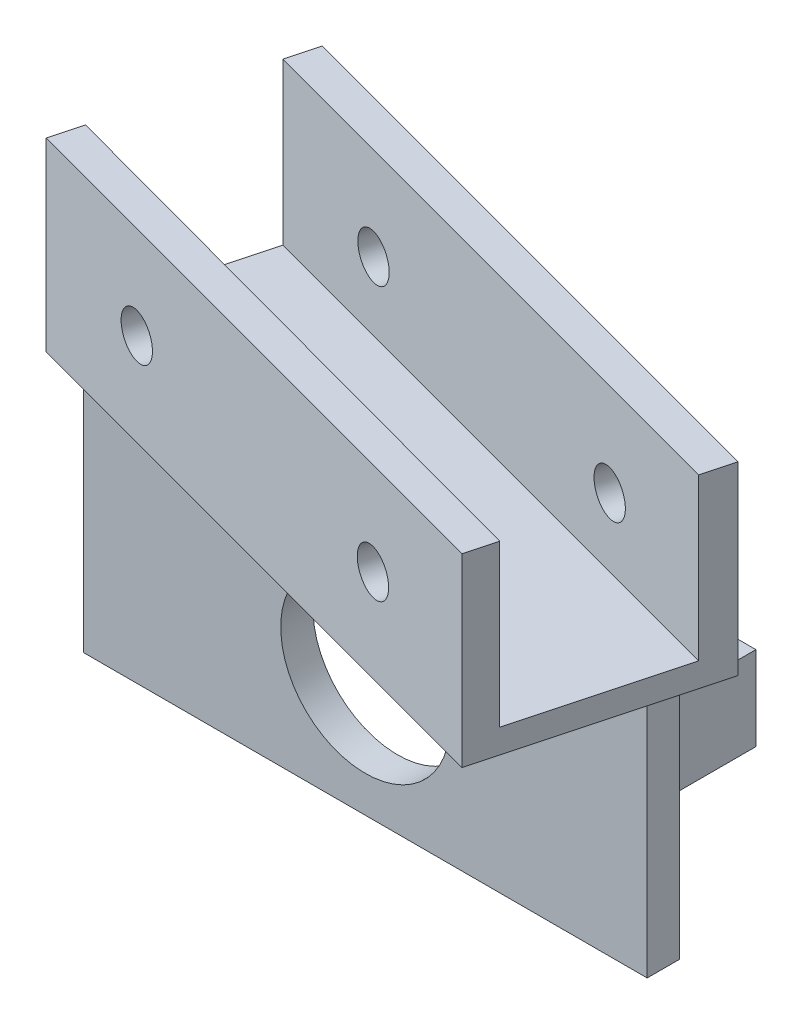
SolidWorks part; units mm, degrees
ref_plane "Front Plane" through (0, 0, 0) normal (0, 0, 1) x (1, 0, 0)
ref_plane "Top Plane" through (0, 0, 0) normal (0, 1, 0) x (1, 0, 0)
ref_plane "Right Plane" through (0, 0, 0) normal (1, 0, 0) x (0, 0, -1)
sketch "Sketch1" plane through (0, 0, 0) normal (0, 0, 1) x (1, 0, 0)
  line L1 (0, 0) -> (70, 0)
  line L2 (0, 0) -> (0, -30)
  line L3 (0, -30) -> (70, -30)
  line L4 (70, 0) -> (70, -30)
  circle A0 centre (35, -15) radius 10.5
  point P7 (70, -15)
  point P8 (35, -30)
  dimension "D1" = 21
  dimension "D2" = 30
  dimension "D3" = 70
extrude "Boss-Extrude1" add sketch "Sketch1" along normal blind 4
sketch "Sketch3" plane through (0, 0, 0) normal (0, 0, -1) x (-1, 0, 0)
  line L0 (-62.5, -8.9384) -> (-54.349, -8.9384)
  line L1 (-54.349, -8.9384) -> (-54.349, -19.3738)
  line L2 (-54.349, -19.3738) -> (-62.5, -19.3738)
  line L3 (-7.5, -5) -> (-14.3209, -5)
  line L4 (-7.5, -25) -> (-7.5, -5)
  line L5 (-62.5, -25) -> (-7.5, -25)
  line L6 (-62.5, -5) -> (-62.5, -25)
  line L7 (-7.5, -5) -> (-62.5, -5)
  line L8 (-7.5, -25) -> (-7.5, -5)
  line L10 (-62.5, -8.9384) -> (-62.5, -19.3738)
  line L12 (-14.3209, -5) -> (-14.3209, -25)
  line L13 (-14.3209, -25) -> (-7.5, -25)
  dimension "D1" = 0
extrude "Boss-Extrude2" add sketch "Sketch3" along normal blind 17
sketch "Sketch4" plane through (0, 0, -17) normal (0, 0, -1) x (-1, 0, 0)
  circle A0 centre (-58.5, -14.2891) radius 1 construction
  circle A1 centre (-58.5, -14.2891) radius 1
  circle A2 centre (-11.5, -7) radius 1 construction
  circle A3 centre (-11.5, -7) radius 1
  circle A4 centre (-11.5, -23) radius 1 construction
  circle A5 centre (-11.5, -23) radius 1
extrude "Cut-Extrude1" cut sketch "Sketch4" against normal blind 17
sketch "Sketch7" plane through (0, 0, 0) normal (0, 1, 0) x (1, 0, 0)
  line L1 (-4.6304, -4) -> (65.8822, -22.8938)
  line L2 (65.8822, -22.8938) -> (73.1291, 4.1521)
  line L5 (-4.6304, -4) -> (2.6166, 23.0459)
  line L8 (70, -4) -> (0, -4) construction
  line L9 (73.1291, 4.1521) -> (2.6166, 23.0459)
  dimension "D1" = 28
  dimension "D2" = 15
  dimension "D3" = 73
extrude "Boss-Extrude4" add sketch "Sketch7" along normal blind 3
sketch "Sketch9" plane through (0, 3, 0) normal (0, 1, 0) x (1, 0, 0)
  line L0 (-4.6304, -4) -> (65.8822, -22.8938)
  line L1 (65.8822, -22.8938) -> (66.8754, -19.1873)
  line L2 (65.8822, -22.8938) -> (73.1291, 4.1521) construction
  line L3 (66.8754, -19.1873) -> (-3.5951, -0.1363)
  line L4 (2.6166, 23.0459) -> (-4.6304, -4) construction
  line L5 (-3.5951, -0.1363) -> (-4.6304, -4)
  line L6 (2.6166, 23.0459) -> (1.5813, 19.1822)
  line L7 (1.5813, 19.1822) -> (72.0939, 0.2884)
  line L8 (72.0939, 0.2884) -> (73.1291, 4.1521)
  line L9 (73.1291, 4.1521) -> (2.6166, 23.0459)
  dimension "D1" = 4
  dimension "D2" = 4
extrude "Boss-Extrude5" add sketch "Sketch9" along normal blind 20
sketch "Sketch10" plane through (5.9368, 0, -22.1563) normal (0.2588, 0, -0.9659) x (-0.9659, 0, -0.2588)
  line L0 (-69.5627, 23) -> (-69.5627, 0) construction
  circle A0 centre (-53.9537, 11.5) radius 2.75
  circle A1 centre (-12.4883, 11.5) radius 2.75
  point P6 (-69.5627, 11.5)
  dimension "D1" = 5.5
  dimension "D2" = 5.5
extrude "Cut-Extrude2" cut sketch "Sketch10" against normal through all
sketch "Sketch11" plane through (-1.3102, 0, 4.8896) normal (-0.2588, 0, 0.9659) x (0.9659, 0, 0.2588)
  point P0 (-29.9311, 14.1586)
